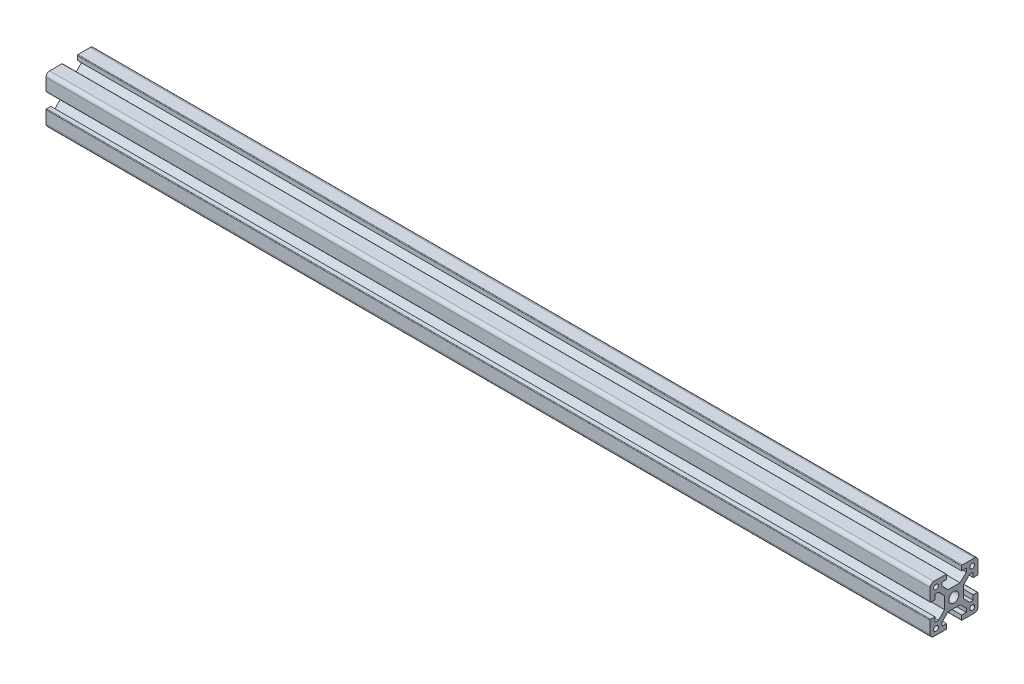
SolidWorks part; units mm, degrees
material "Alumina"
ref_plane "Front Plane" through (0, 0, 0) normal (0, 0, 1) x (1, 0, 0)
ref_plane "Top Plane" through (0, 0, 0) normal (0, 1, 0) x (1, 0, 0)
ref_plane "Right Plane" through (0, 0, 0) normal (1, 0, 0) x (0, 0, -1)
sketch "Sketch1" plane through (0, 0, 0) normal (0, 1, 0) x (1, 0, 0)
  line L0 (0, 0) -> (400, 0)
other "Xa XA-2020T(1)"
ref_plane "Plane1" through (0, 0, 0) normal (1, 0, 0) x (0, 0, -1)
sketch "Sketch11" plane through (0, 0, 0) normal (1, 0, 0) x (0, 0, -1)
  line L0 (-9.8891, 9.9394) -> (10.1109, -10.0606) construction
  line L1 (-9.8891, 9.9394) -> (10.1109, 9.9394) construction
  line L2 (-9.8891, 9.9394) -> (-9.8891, -10.0606) construction
  line L3 (-9.8891, -10.0606) -> (10.1109, -10.0606) construction
  line L4 (10.1109, 9.9394) -> (10.1109, -10.0606) construction
  line L5 (-9.8891, -10.0606) -> (10.1109, 9.9394) construction
  line L6 (0.1109, 9.9394) -> (0.1109, -10.0606) construction
  line L7 (10.1109, -0.0606) -> (-9.8891, -0.0606) construction
  line L88 (-9.8891, 8.4394) -> (-9.8891, 3.2894)
  line L89 (-9.6391, 3.0394) -> (-7.8891, 3.0394)
  line L90 (-7.8891, 3.0394) -> (-7.8891, 5.0394)
  line L91 (-7.8891, 5.0394) -> (-6.4169, 5.0394)
  line L92 (-6.4169, 5.0394) -> (-3.8891, 2.4394)
  line L93 (-3.8891, 2.4394) -> (-3.8891, -2.5606)
  line L94 (-3.8891, -2.5606) -> (-6.4169, -5.1606)
  line L95 (-6.4169, -5.1606) -> (-7.8891, -5.1606)
  line L96 (-7.8891, -5.1606) -> (-7.8891, -3.1606)
  line L97 (-7.8891, -3.1606) -> (-9.6391, -3.1606)
  line L98 (-9.8891, -3.4106) -> (-9.8891, -8.5606)
  line L99 (-8.3891, -10.0606) -> (-3.2391, -10.0606)
  line L100 (-2.9891, -9.8106) -> (-2.9891, -8.0606)
  line L101 (-2.9891, -8.0606) -> (-4.9891, -8.0606)
  line L102 (-4.9891, -8.0606) -> (-4.9891, -6.5883)
  line L103 (-4.9891, -6.5883) -> (-2.3891, -4.0606)
  line L104 (-2.3891, -4.0606) -> (2.6109, -4.0606)
  line L105 (2.6109, -4.0606) -> (5.2109, -6.5883)
  line L106 (5.2109, -6.5883) -> (5.2109, -8.0606)
  line L107 (5.2109, -8.0606) -> (3.2109, -8.0606)
  line L108 (3.2109, -8.0606) -> (3.2109, -9.8106)
  line L109 (3.4609, -10.0606) -> (8.6109, -10.0606)
  line L110 (10.1109, -8.5606) -> (10.1109, -3.4106)
  line L111 (9.8609, -3.1606) -> (8.1109, -3.1606)
  line L112 (8.1109, -3.1606) -> (8.1109, -5.1606)
  line L113 (8.1109, -5.1606) -> (6.6387, -5.1606)
  line L114 (6.6387, -5.1606) -> (4.1109, -2.5606)
  line L115 (4.1109, -2.5606) -> (4.1109, 2.4394)
  line L116 (4.1109, 2.4394) -> (6.6387, 5.0394)
  line L117 (6.6387, 5.0394) -> (8.1109, 5.0394)
  line L118 (8.1109, 5.0394) -> (8.1109, 3.0394)
  line L119 (8.1109, 3.0394) -> (9.8609, 3.0394)
  line L120 (10.1109, 3.2894) -> (10.1109, 8.4394)
  line L121 (8.6109, 9.9394) -> (3.4609, 9.9394)
  line L122 (3.2109, 9.6894) -> (3.2109, 7.9394)
  line L123 (3.2109, 7.9394) -> (5.2109, 7.9394)
  line L124 (5.2109, 7.9394) -> (5.2109, 6.4672)
  line L125 (5.2109, 6.4672) -> (2.6109, 3.9394)
  line L126 (2.6109, 3.9394) -> (-2.3891, 3.9394)
  line L127 (-2.3891, 3.9394) -> (-4.9891, 6.4672)
  line L128 (-4.9891, 6.4672) -> (-4.9891, 7.9394)
  line L129 (-4.9891, 7.9394) -> (-2.9891, 7.9394)
  line L130 (-2.9891, 7.9394) -> (-2.9891, 9.6894)
  line L131 (-3.2391, 9.9394) -> (-8.3891, 9.9394)
  circle A0 centre (-7.4391, 7.4894) radius 1
  circle A1 centre (7.6609, 7.4894) radius 1
  circle A2 centre (-7.4391, -7.6106) radius 1
  circle A3 centre (7.6609, -7.6106) radius 1
  circle A4 centre (0, 0) radius 2.1
  arc A26 (-9.8891, 3.2894) -> (-9.6391, 3.0394) centre (-9.6391, 3.2894) ccw
  arc A27 (-9.6391, -3.1606) -> (-9.8891, -3.4106) centre (-9.6391, -3.4106) ccw
  arc A28 (-9.8891, -8.5606) -> (-8.3891, -10.0606) centre (-8.3891, -8.5606) ccw
  arc A29 (-3.2391, -10.0606) -> (-2.9891, -9.8106) centre (-3.2391, -9.8106) ccw
  arc A30 (3.2109, -9.8106) -> (3.4609, -10.0606) centre (3.4609, -9.8106) ccw
  arc A31 (8.6109, -10.0606) -> (10.1109, -8.5606) centre (8.6109, -8.5606) ccw
  arc A32 (10.1109, -3.4106) -> (9.8609, -3.1606) centre (9.8609, -3.4106) ccw
  arc A33 (9.8609, 3.0394) -> (10.1109, 3.2894) centre (9.8609, 3.2894) ccw
  arc A34 (10.1109, 8.4394) -> (8.6109, 9.9394) centre (8.6109, 8.4394) ccw
  arc A35 (3.4609, 9.9394) -> (3.2109, 9.6894) centre (3.4609, 9.6894) ccw
  arc A36 (-2.9891, 9.6894) -> (-3.2391, 9.9394) centre (-3.2391, 9.6894) ccw
  arc A37 (-8.3891, 9.9394) -> (-9.8891, 8.4394) centre (-8.3891, 8.4394) ccw
  point P52 (0, 0)
ref_plane "Plane2" through (400, 6.4672, 4.9891) normal (0, 0.6971, 0.717) x (1, 0, 0)
sketch "Sketch14" plane through (400, 0, 0) normal (1, 0, 0) x (0, 0, -1)
  line L1 (-12.9827, 12.3363) -> (12.9827, 12.3363)
  line L2 (-12.9827, 12.3363) -> (-12.9827, -12.3363)
  line L3 (-12.9827, -12.3363) -> (12.9827, -12.3363)
  line L4 (12.9827, 12.3363) -> (12.9827, -12.3363)
  line L5 (-12.9827, 12.3363) -> (12.9827, -12.3363) construction
  line L6 (-12.9827, -12.3363) -> (12.9827, 12.3363) construction
  point P0 (0, 0)
extrude "Cut-Extrude2" cut sketch "Sketch14" against normal blind 30
